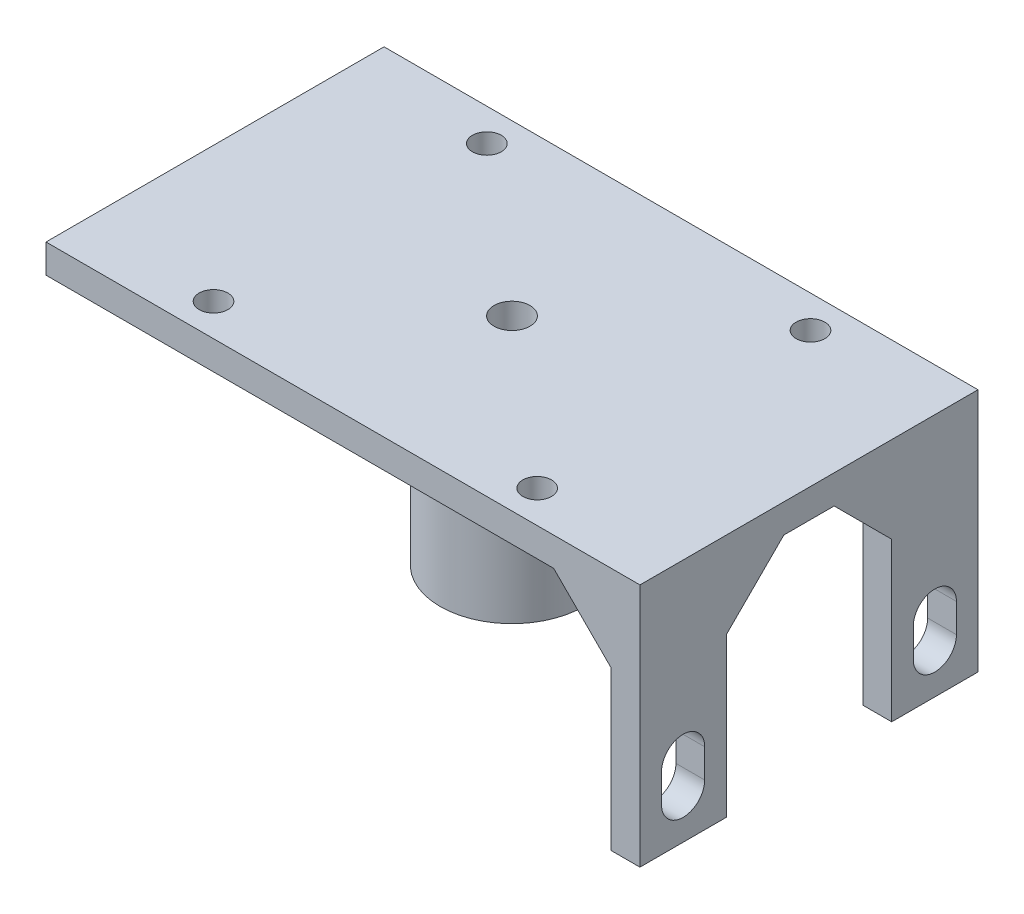
SolidWorks part; units mm, degrees
ref_plane "Alzado" through (0, 0, 0) normal (0, 0, 1) x (1, 0, 0)
ref_plane "Planta" through (0, 0, 0) normal (0, 1, 0) x (1, 0, 0)
ref_plane "Vista lateral" through (0, 0, 0) normal (1, 0, 0) x (0, 0, -1)
ref_plane "Plano1" through (41.2905, 0, 0) normal (-1, 0, 0) x (0, 0, 1)
sketch "Croquis3" plane through (41.2905, 0, 0) normal (-1, 0, 0) x (0, 0, 1)
  line L2 (17.5, -19.99) -> (17.5, -23.99) construction
  line L3 (20.5, -19.99) -> (20.5, -23.99)
  line L4 (14.5, -19.99) -> (14.5, -23.99)
  line L5 (0, 0) -> (0, -196.5902) construction
  line L6 (-17.5, -19.99) -> (-17.5, -23.99) construction
  line L7 (11.5, 0) -> (23.5, 0)
  line L8 (11.5, 0) -> (11.5, -29.99)
  line L9 (11.5, -29.99) -> (23.5, -29.99)
  line L10 (23.5, 0) -> (23.5, -29.99)
  line L11 (-20.5, -19.99) -> (-20.5, -23.99)
  line L12 (-14.5, -19.99) -> (-14.5, -23.99)
  line L13 (-23.5, 0) -> (-23.5, -29.99)
  line L14 (-11.5, -29.99) -> (-23.5, -29.99)
  line L15 (-11.5, 0) -> (-11.5, -29.99)
  line L16 (-11.5, 0) -> (-23.5, 0)
  arc A4 (20.5, -19.99) -> (14.5, -19.99) centre (17.5, -19.99) ccw
  arc A5 (14.5, -23.99) -> (20.5, -23.99) centre (17.5, -23.99) ccw
  arc A6 (-20.5, -19.99) -> (-14.5, -19.99) centre (-17.5, -19.99) cw
  arc A7 (-14.5, -23.99) -> (-20.5, -23.99) centre (-17.5, -23.99) cw
  circle A9 centre (17.5, -21.99) radius 2.075 construction
  circle A10 centre (-17.5, -21.99) radius 2.075 construction
  circle A11 centre (17.5, -21.99) radius 2.075
  circle A12 centre (-17.5, -21.99) radius 2.075
  point P10 (17.5, -21.99)
  point P25 (-17.5, -21.99)
  dimension "D2" = 3
  dimension "D1" = 4
  dimension "D3" = 3
  dimension "D4" = 12
  dimension "D5" = 6
extrude "Saliente-Extruir1" add sketch "Croquis3" along normal blind 4 separate body contours L10 L7 L8 L9 A5 L4 A4 L3 | L15 L16 L13 L14 L12 A7 L11 A6
sketch "Croquis4" plane through (0, 0, 0) normal (0, 1, 0) x (1, 0, 0)
  line L0 (41.2905, 11.5) -> (41.2905, 23.5) construction
  line L1 (41.2905, -23.5) -> (-41.2905, -23.5)
  line L2 (41.2905, -23.5) -> (41.2905, 23.5)
  line L3 (41.2905, 23.5) -> (-41.2905, 23.5)
  line L4 (-41.2905, -23.5) -> (-41.2905, 23.5)
  point P8 (0, -23.5)
extrude "Saliente-Extruir2" add sketch "Croquis4" along normal blind 4 and the other way blind 0.0001
sketch "Croquis2" plane through (0, 0, 0) normal (0, 0, 1) x (1, 0, 0)
  line L0 (-10, -0.0001) -> (-10, -26)
  line L1 (-10, -26) -> (-2.5, -26)
  line L2 (0, 0) -> (0, -201.8724) construction
  line L3 (-2.5, -0.0001) -> (-10, -0.0001)
  line L4 (-2.5, -0.0001) -> (-2.5, -26)
  line L5 (37.2905, -0.0001) -> (41.2905, -0.0001) construction
  dimension "D1" = 20
  dimension "D2" = 5
revolve "Revolución2" add sketch "Croquis2" angle 360 about L2
chamfer "Chaflán2" distance 8 angle 45 5 edges at (39.2905, -0.0001, -11.5) (37.2905, -0.0001, -17.5) (0, -0.0001, 10) (39.2905, -0.0001, 11.5) (37.2905, -0.0001, 17.5)
sketch "Croquis5" plane through (0, -0.0001, 0) normal (0, -1, 0) x (1, 0, 0)
  line L1 (-22.5, 19) -> (22.5, 19) construction
  line L2 (-22.5, 19) -> (-22.5, -19) construction
  line L3 (-22.5, -19) -> (22.5, -19) construction
  line L4 (22.5, 19) -> (22.5, -19) construction
  circle A0 centre (-22.5, 19) radius 2
  circle A1 centre (22.5, 19) radius 2
  circle A2 centre (22.5, -19) radius 2
  circle A3 centre (-22.5, -19) radius 2
  circle A4 centre (0, 0) radius 2.5 construction
  circle A5 centre (0, 0) radius 2.5
  point P4 (0, 19)
  point P6 (-22.5, 0)
  dimension "D1" = 4
  dimension "D2" = 45
  dimension "D3" = 38
extrude "Cortar-Extruir1" cut sketch "Croquis5" against normal through all both and the other way through all
